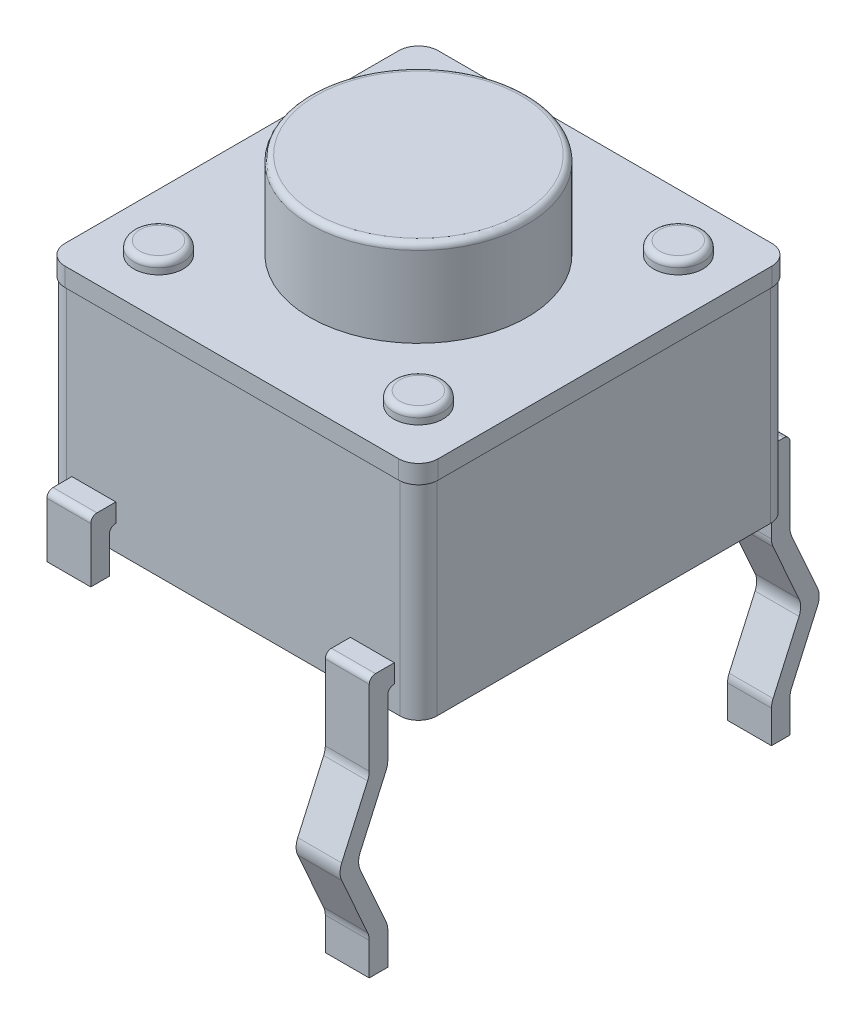
SolidWorks part; units mm, degrees
ref_plane "Plano frontal" through (0, 0, 0) normal (0, 0, 1) x (1, 0, 0)
ref_plane "Plano superior" through (0, 0, 0) normal (0, 1, 0) x (1, 0, 0)
ref_plane "Plano direito" through (0, 0, 0) normal (1, 0, 0) x (0, 0, -1)
sketch "Esboço1" plane through (0, 0, 0) normal (0, 1, 0) x (1, 0, 0)
  line L1 (-2.695, 2.995) -> (2.695, 2.995)
  line L2 (-2.995, 2.695) -> (-2.995, -2.695)
  line L3 (-2.695, -2.995) -> (2.695, -2.995)
  line L4 (2.995, 2.695) -> (2.995, -2.695)
  line L5 (-2.995, 2.995) -> (2.995, -2.995) construction
  line L6 (-2.995, -2.995) -> (2.995, 2.995) construction
  arc A0 (-2.995, -2.695) -> (-2.695, -2.995) centre (-2.695, -2.695) ccw
  arc A1 (2.695, -2.995) -> (2.995, -2.695) centre (2.695, -2.695) ccw
  arc A2 (2.695, 2.995) -> (2.995, 2.695) centre (2.695, 2.695) cw
  arc A3 (-2.695, 2.995) -> (-2.995, 2.695) centre (-2.695, 2.695) ccw
  point P0 (0, 0)
  dimension "D3" = 0.3
  dimension "D1" = 5.99
  dimension "D2" = 5.99
extrude "Ressalto-extrusão1" add sketch "Esboço1" along normal blind 3.61
sketch "Esboço2" plane through (0, 3.61, 0) normal (0, 1, 0) x (1, 0, 0)
  circle A0 centre (0, 0) radius 1.755
  dimension "D1" = 3.51
extrude "Ressalto-extrusão2" add sketch "Esboço2" along normal blind 1.4 separate body
fillet "Filete1" radius 0.1 1 edges at (0, 5.01, 1.755)
sketch "Esboço3" plane through (0, 3.61, 0) normal (0, 1, 0) x (1, 0, 0)
  line L0 (0, 0) -> (0, 2.995) construction
  line L1 (2.695, 2.995) -> (-2.695, 2.995) construction
  line L2 (0, 0) -> (-2.995, 0) construction
  line L3 (-2.995, 2.695) -> (-2.995, -2.695) construction
  circle A0 centre (-2.1, 2.1) radius 0.4
  circle A1 centre (2.1, 2.1) radius 0.4
  circle A2 centre (2.1, -2.1) radius 0.4
  circle A3 centre (-2.1, -2.1) radius 0.4
  dimension "D3" = 0.8
  dimension "D1" = 2.1
  dimension "D2" = 2.1
extrude "Ressalto-extrusão3" add sketch "Esboço3" along normal blind 0.2
fillet "Filete2" radius 0.1 4 edges at (2.1, 3.81, -2.5) (2.1, 3.81, 2.5) (-2.1, 3.81, -1.7) (-2.1, 3.81, 1.7)
sketch "Esboço4" plane through (0, 3.61, 0) normal (0, 1, 0) x (1, 0, 0)
  line L8 (-2.695, -3.015) -> (2.695, -3.015)
  line L9 (3.015, -2.695) -> (3.015, 2.695)
  line L10 (2.695, 3.015) -> (-2.695, 3.015)
  line L11 (-3.015, 2.695) -> (-3.015, -2.695)
  line L12 (-2.695, -3.015) -> (2.695, -3.015)
  line L13 (3.015, -2.695) -> (3.015, 2.695)
  line L14 (2.695, 3.015) -> (-2.695, 3.015)
  line L15 (-3.015, 2.695) -> (-3.015, -2.695)
  arc A8 (-3.015, -2.695) -> (-2.695, -3.015) centre (-2.695, -2.695) ccw
  arc A9 (2.695, -3.015) -> (3.015, -2.695) centre (2.695, -2.695) ccw
  arc A10 (3.015, 2.695) -> (2.695, 3.015) centre (2.695, 2.695) ccw
  arc A11 (-2.695, 3.015) -> (-3.015, 2.695) centre (-2.695, 2.695) ccw
  arc A12 (-3.015, -2.695) -> (-2.695, -3.015) centre (-2.695, -2.695) ccw
  arc A13 (2.695, -3.015) -> (3.015, -2.695) centre (2.695, -2.695) ccw
  arc A14 (3.015, 2.695) -> (2.695, 3.015) centre (2.695, 2.695) ccw
  arc A15 (-2.695, 3.015) -> (-3.015, 2.695) centre (-2.695, 2.695) ccw
  dimension "D1" = 0.02
extrude "Ressalto-extrusão4" add sketch "Esboço4" against normal blind 0.3
ref_plane "Plano1" through (2.25, 0, 0) normal (1, 0, 0) x (0, 0, -1)
sketch "Esboço5" plane through (2.25, 0, 0) normal (1, 0, 0) x (0, 0, -1)
  line L0 (3.25, -3.51) -> (3.25, 5.3695) construction
  line L1 (2.995, 0.4) -> (3, 0.4)
  line L2 (2.995, 3.31) -> (2.995, 0) construction
  line L3 (3.1, 0.3) -> (3.1, -0.6161)
  line L4 (3.1261, -0.7384) -> (3.5454, -1.6777)
  line L5 (3.5454, -1.9223) -> (3.1261, -2.8616)
  line L6 (3.1, -2.9839) -> (3.1, -3.51)
  line L7 (2.995, 0.7) -> (3.3, 0.7)
  line L8 (3.4, 0.6) -> (3.4, -0.6161)
  line L9 (3.4261, -0.7384) -> (3.8454, -1.6777)
  line L10 (3.8454, -1.9223) -> (3.4261, -2.8616)
  line L11 (3.4, -2.9839) -> (3.4, -3.51)
  line L12 (3.4, -3.51) -> (3.1, -3.51)
  line L13 (2.695, 0) -> (2.995, 0) construction
  line L14 (-2.695, 0) -> (2.695, 0) construction
  line L15 (2.995, 0.4) -> (2.995, 0.7)
  arc A0 (3.1261, -2.8616) -> (3.1, -2.9839) centre (3.4, -2.9839) ccw
  arc A1 (3.4261, -2.8616) -> (3.4, -2.9839) centre (3.7, -2.9839) ccw
  arc A2 (3.5454, -1.6777) -> (3.5454, -1.9223) centre (3.2715, -1.8) cw
  arc A3 (3.8454, -1.6777) -> (3.8454, -1.9223) centre (3.5715, -1.8) cw
  arc A4 (3.4, -0.6161) -> (3.4261, -0.7384) centre (3.7, -0.6161) ccw
  arc A5 (3.1, -0.6161) -> (3.1261, -0.7384) centre (3.4, -0.6161) ccw
  arc A6 (3.3, 0.7) -> (3.4, 0.6) centre (3.3, 0.6) cw
  arc A7 (3, 0.4) -> (3.1, 0.3) centre (3, 0.3) cw
  point P28 (3.6, -1.8)
  point P31 (3.9, -1.8)
  point P34 (3.4, -0.68)
  dimension "D11" = 0.3
  dimension "D12" = 0.1
  dimension "D1" = 3.25
  dimension "D2" = 0.3
  dimension "D3" = 0.3
  dimension "D4" = 0.3
  dimension "D5" = 0.3
  dimension "D6" = 0.68
  dimension "D7" = 3.51
  dimension "D8" = 1.8
  dimension "D9" = 3.9
  dimension "D10" = 0.7
extrude "Ressalto-extrusão5" add sketch "Esboço5" along normal blind 0.355 and the other way blind 0.355
mirror "Espelhar1" about plane through (0, 0, 0) normal (1, 0, 0) of "Ressalto-extrusão5"
mirror "Espelhar2" about plane through (0, 0, 0) normal (0, 0, 1) of "Espelhar1", "Ressalto-extrusão5"
sketch "Sketch1" plane through (0, -3.51, 0) normal (0, -1, 0) x (1, 0, 0)
  circle A0 centre (-2.2083, 3.2624) radius 1.1373
extrude "Cut-Extrude1" cut sketch "Sketch1" against normal up to surface (3.222 mm away)
